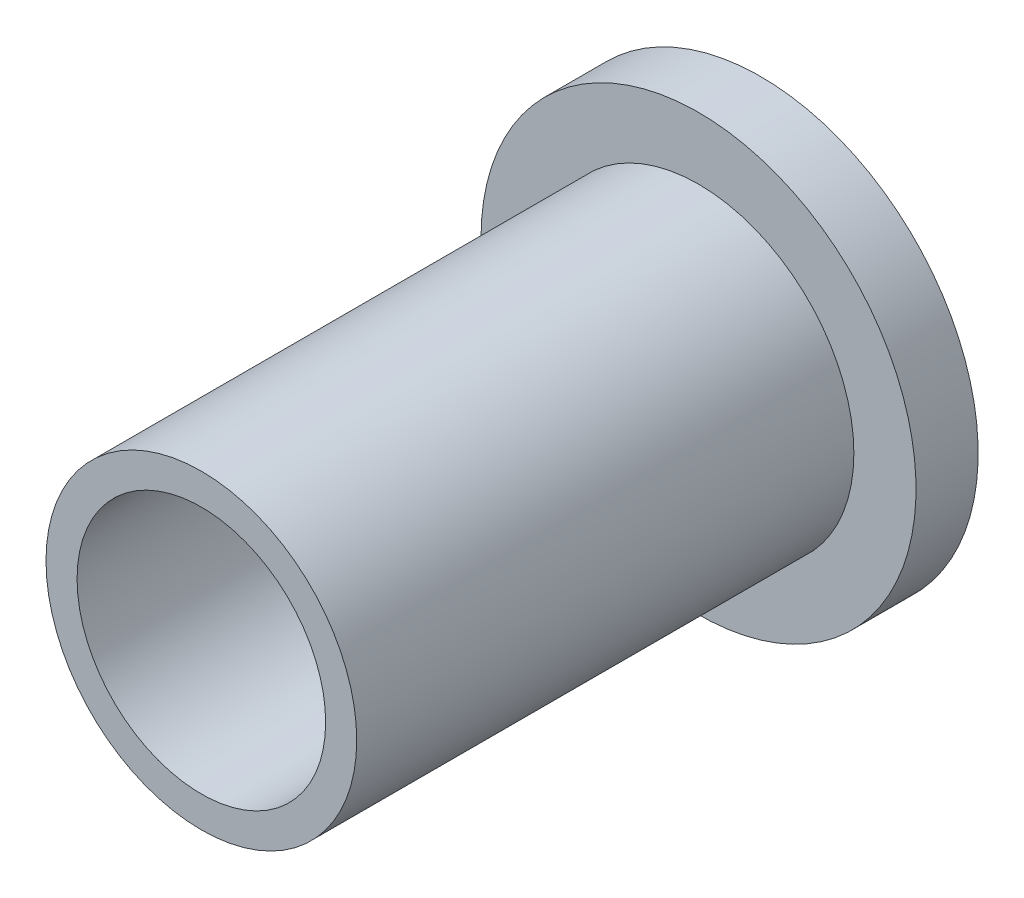
SolidWorks part; units mm, degrees
material "Aluminum Bronze"
ref_plane "Front Plane" through (0, 0, 0) normal (0, 0, 1) x (1, 0, 0)
ref_plane "Top Plane" through (0, 0, 0) normal (0, 1, 0) x (1, 0, 0)
ref_plane "Right Plane" through (0, 0, 0) normal (1, 0, 0) x (0, 0, -1)
sketch "Sketch1" plane through (0, 0, 0) normal (0, 0, 1) x (1, 0, 0)
  circle A0 centre (0, 0) radius 6.35
  circle A1 centre (0, 0) radius 7.9375
  dimension "D1" = 12.7
  dimension "D2" = 15.875
extrude "Boss-Extrude1" add sketch "Sketch1" along normal blind 25.4
sketch "Sketch2" plane through (0, 0, 0) normal (0, 0, -1) x (-1, 0, 0)
  circle A0 centre (0, 0) radius 6.35 construction
  circle A1 centre (0, 0) radius 11.1125
  circle A3 centre (0, 0) radius 6.35
  dimension "D1" = 22.225
extrude "Boss-Extrude2" add sketch "Sketch2" along normal blind 3.175
